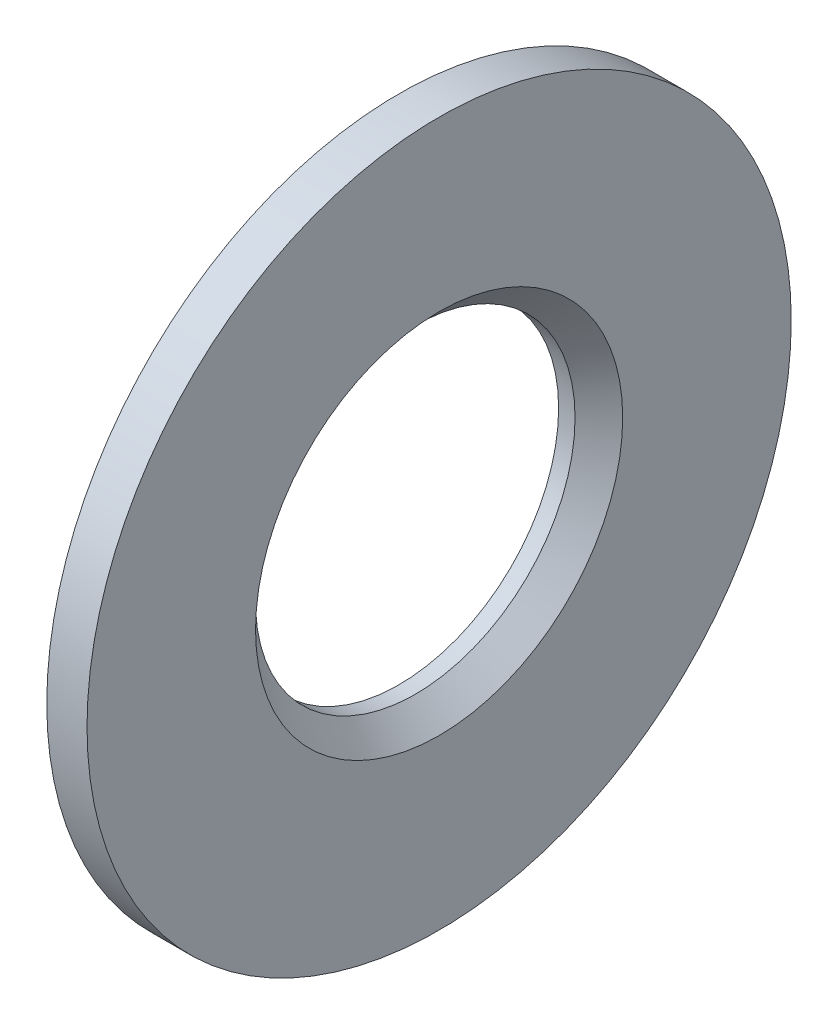
SolidWorks part; units mm, degrees
material "Plain Carbon Steel"
ref_plane "Front Plane" through (0, 0, 0) normal (0, 0, 1) x (1, 0, 0)
ref_plane "Top Plane" through (0, 0, 0) normal (0, 1, 0) x (1, 0, 0)
ref_plane "Right Plane" through (0, 0, 0) normal (1, 0, 0) x (0, 0, -1)
sketch "Sketch1" plane through (0, 0, 0) normal (1, 0, 0) x (0, 0, -1)
  circle A1 centre (0, 0) radius 11.1125
  dimension "D1" = 22.225
extrude "Boss-Extrude1" add sketch "Sketch1" along normal blind 1.27
hole_wizard "3/8 Clearance Hole1" positions "Sketch3" profile "Sketch2" hole size "3/8" standard "ANSI Inch" end condition through all
sketch "Sketch3" plane through (1.27, 0, 0) normal (1, 0, 0) x (0, 0, -1)
  point P0 (0, 0)
sketch "Sketch2" plane through (1.27, 0, 0) normal (0, 1, 0) x (0, 0, -1)
  line L0 (0, 0) -> (0, 1.27)
  line L1 (0, 1.27) -> (5.0419, 1.27)
  line L2 (5.0419, 1.27) -> (5.0419, 0.7518)
  line L3 (5.0419, 0.7518) -> (5.7937, 0)
  line L5 (5.7937, 0) -> (0, 0)
  line L6 (-5.0419, 0.7518) -> (-5.7937, 0) construction
  line L11 (0, -6.35) -> (0, 107.95) construction
  dimension "Thru Hole Dia." = 10.0838
  dimension "Thru Hole Depth" = 1.27
  dimension "Near C'Sink Dia." = 11.5875
  dimension "Near C'Sink Angle" = 90
